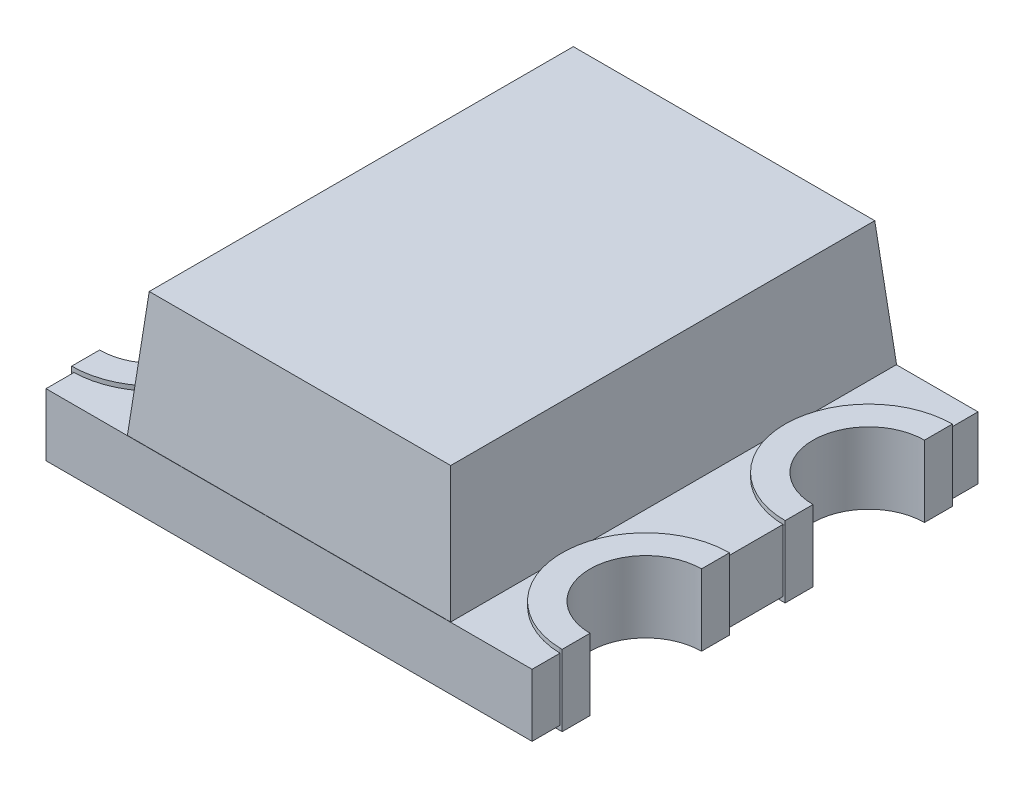
SolidWorks part; units mm, degrees
ref_plane "Front Plane" through (0, 0, 0) normal (0, 0, 1) x (1, 0, 0)
ref_plane "Top Plane" through (0, 0, 0) normal (0, 1, 0) x (1, 0, 0)
ref_plane "Right Plane" through (0, 0, 0) normal (1, 0, 0) x (0, 0, -1)
sketch "Sketch1" plane through (0, 0, 0) normal (0, 1, 0) x (1, 0, 0)
  line L1 (1.1, 1) -> (-1.1, 1)
  line L2 (1.1, 1) -> (1.1, -1)
  line L3 (1.1, -1) -> (-1.1, -1)
  line L4 (-1.1, 1) -> (-1.1, -1)
  line L5 (1.1, 1) -> (-1.1, -1) construction
  line L6 (1.1, -1) -> (-1.1, 1) construction
  point P0 (0, 0)
  dimension "D1" = 2
  dimension "D2" = 2.2
extrude "Boss-Extrude1" add sketch "Sketch1" along normal blind 0.28
sketch "Sketch2" plane through (0, 0.28, 0) normal (0, 1, 0) x (1, 0, 0)
  line L0 (-1.1, 1) -> (-1.1, -1) construction
  line L1 (-1.1, 0.875) -> (-0.565, 0.875)
  line L2 (-1.1, 0.875) -> (-1.1, 0.125)
  line L3 (-1.1, 0.125) -> (-0.565, 0.125)
  line L4 (-0.565, 0.875) -> (-0.565, 0.125)
  line L5 (0, 0) -> (0, 0.3307) construction
  line L6 (0, 0) -> (0.4542, 0) construction
  line L7 (0.565, 0.875) -> (0.565, 0.125)
  line L8 (1.1, 0.125) -> (0.565, 0.125)
  line L9 (1.1, 0.875) -> (1.1, 0.125)
  line L10 (1.1, 0.875) -> (0.565, 0.875)
  line L11 (1.1, -0.875) -> (0.565, -0.875)
  line L12 (1.1, -0.875) -> (1.1, -0.125)
  line L13 (1.1, -0.125) -> (0.565, -0.125)
  line L14 (0.565, -0.875) -> (0.565, -0.125)
  line L15 (-0.565, -0.875) -> (-0.565, -0.125)
  line L16 (-1.1, -0.125) -> (-0.565, -0.125)
  line L17 (-1.1, -0.875) -> (-1.1, -0.125)
  line L18 (-1.1, -0.875) -> (-0.565, -0.875)
  circle A0 centre (-1.1, 0.5) radius 0.25
  circle A1 centre (1.1, 0.5) radius 0.25
  circle A2 centre (1.1, -0.5) radius 0.25
  circle A3 centre (-1.1, -0.5) radius 0.25
  point P9 (-0.565, 0.5)
  line M5 (-1.1, 1) -> (-1.1, -1)
  line M7 (1.1, -1) -> (1.1, 1)
  dimension "D3" = 0.535
  dimension "D4" = 0.5
  dimension "D1" = 0.5
  dimension "D2" = 0.75
extrude "Boss-Extrude2" add sketch "Sketch2" along normal blind 0.02 contours A0 L3 L4 L1 M5 | A1 L10 L7 L8 M7 | A2 L13 L14 L11 M7 | A3 L18 L15 L16 M5
sketch "Sketch3" plane through (0, 0.28, 0) normal (0, 1, 0) x (1, 0, 0)
  line L1 (-1.1, 0.75) -> (-1.1, 0.25)
  line L2 (-1.1, 0.75) -> (-1.1, 0.25)
  line L3 (-1.1, -0.25) -> (-1.1, -0.75)
  line L4 (-1.1, -0.25) -> (-1.1, -0.75)
  line L5 (1.1, 0.25) -> (1.1, 0.75)
  line L6 (1.1, 0.25) -> (1.1, 0.75)
  line L7 (1.1, -0.75) -> (1.1, -0.25)
  line L8 (1.1, -0.75) -> (1.1, -0.25)
  arc A1 (-1.1, 0.25) -> (-1.1, 0.75) centre (-1.1, 0.5) ccw
  arc A2 (-1.1, 0.25) -> (-1.1, 0.75) centre (-1.1, 0.5) ccw
  arc A3 (-1.1, -0.75) -> (-1.1, -0.25) centre (-1.1, -0.5) ccw
  arc A4 (-1.1, -0.75) -> (-1.1, -0.25) centre (-1.1, -0.5) ccw
  arc A5 (1.1, 0.75) -> (1.1, 0.25) centre (1.1, 0.5) ccw
  arc A6 (1.1, 0.75) -> (1.1, 0.25) centre (1.1, 0.5) ccw
  arc A7 (1.1, -0.25) -> (1.1, -0.75) centre (1.1, -0.5) ccw
  arc A8 (1.1, -0.25) -> (1.1, -0.75) centre (1.1, -0.5) ccw
  dimension "D1" = 0
  dimension "D2" = 0
  dimension "D3" = 0
  dimension "D4" = 0
extrude "Cut-Extrude1" cut sketch "Sketch3" against normal blind 2
sketch "Sketch4" plane through (-1.1, 0, 0) normal (-1, 0, 0) x (0, 0, 1)
  line L0 (-0.875, 0.28) -> (-0.875, 0)
  line L1 (-1, 0) -> (-0.75, 0) construction
  line L2 (-0.125, 0.28) -> (-0.125, 0)
  line L3 (-0.25, 0) -> (0.25, 0) construction
  line L4 (0.125, 0.28) -> (0.125, 0)
  line L5 (-0.125, 0.28) -> (0.125, 0.28) construction
  line L6 (0.875, 0.28) -> (0.875, 0)
  line L7 (0.75, 0) -> (1, 0) construction
  line L14 (-1, 0) -> (-0.75, 0)
  line L15 (-0.75, 0) -> (-0.75, 0.3)
  line L16 (-0.25, 0) -> (0.25, 0)
  line L17 (0.25, 0) -> (0.25, 0.3)
  line L18 (0.25, 0.3) -> (0.125, 0.3)
  line L19 (0.125, 0.3) -> (0.125, 0.28)
  line L20 (0.125, 0.28) -> (-0.125, 0.28)
  line L21 (-0.125, 0.28) -> (-0.125, 0.3)
  line L22 (-0.125, 0.3) -> (-0.25, 0.3)
  line L23 (-0.25, 0.3) -> (-0.25, 0)
  line L24 (-0.25, 0) -> (0.25, 0)
  line L25 (0.25, 0) -> (0.25, 0.3)
  line L26 (0.25, 0.3) -> (0.125, 0.3)
  line L27 (0.125, 0.3) -> (0.125, 0.28)
  line L28 (0.125, 0.28) -> (-0.125, 0.28)
  line L29 (-0.125, 0.28) -> (-0.125, 0.3)
  line L30 (-0.125, 0.3) -> (-0.25, 0.3)
  line L31 (-0.25, 0.3) -> (-0.25, 0)
  line L32 (-0.75, 0.3) -> (-0.875, 0.3)
  line L33 (-0.875, 0.3) -> (-0.875, 0.28)
  line L34 (-0.875, 0.28) -> (-1, 0.28)
  line L35 (-1, 0.28) -> (-1, 0)
  line L36 (-1, 0) -> (-0.75, 0)
  line L37 (-0.75, 0) -> (-0.75, 0.3)
  line L38 (-0.75, 0.3) -> (-0.875, 0.3)
  line L39 (-0.875, 0.3) -> (-0.875, 0.28)
  line L40 (-0.875, 0.28) -> (-1, 0.28)
  line L41 (-1, 0.28) -> (-1, 0)
  line L42 (0.75, 0.3) -> (0.75, 0)
  line L43 (0.75, 0) -> (1, 0)
  line L44 (1, 0) -> (1, 0.28)
  line L45 (1, 0.28) -> (0.875, 0.28)
  line L46 (0.875, 0.28) -> (0.875, 0.3)
  line L47 (0.875, 0.3) -> (0.75, 0.3)
  line L48 (0.75, 0.3) -> (0.75, 0)
  line L49 (0.75, 0) -> (1, 0)
  line L50 (1, 0) -> (1, 0.28)
  line L51 (1, 0.28) -> (0.875, 0.28)
  line L52 (0.875, 0.28) -> (0.875, 0.3)
  line L53 (0.875, 0.3) -> (0.75, 0.3)
  line M21 (-1, 0) -> (-0.75, 0)
  line M25 (-0.875, 0.28) -> (-1, 0.28)
  line M26 (-1, 0.28) -> (-1, 0)
  dimension "D1" = 0
  dimension "D2" = 0
  dimension "D3" = 0
extrude "Cut-Extrude2" cut sketch "Sketch4" against normal blind 0.01 contours L0 M25 M26 M21 | L4 L28 L2 L24 | L50 L51 L6 L49
sketch "Sketch5" plane through (1.1, 0, 0) normal (1, 0, 0) x (0, 0, -1)
  line L0 (-0.875, 0.28) -> (-0.875, 0)
  line L1 (-1, 0) -> (-0.75, 0) construction
  line L2 (-0.125, 0.28) -> (-0.125, 0)
  line L3 (-0.25, 0) -> (0.25, 0) construction
  line L4 (0.125, 0.28) -> (0.125, 0)
  line L5 (0.875, 0.28) -> (0.875, 0)
  line L6 (0.75, 0) -> (1, 0) construction
  line L13 (-1, 0) -> (-0.75, 0)
  line L14 (-0.75, 0) -> (-0.75, 0.3)
  line L15 (-0.75, 0.3) -> (-0.875, 0.3)
  line L16 (-0.875, 0.3) -> (-0.875, 0.28)
  line L17 (-0.875, 0.28) -> (-1, 0.28)
  line L18 (-1, 0.28) -> (-1, 0)
  line L19 (-1, 0) -> (-0.75, 0)
  line L20 (-0.75, 0) -> (-0.75, 0.3)
  line L21 (-0.75, 0.3) -> (-0.875, 0.3)
  line L22 (-0.875, 0.3) -> (-0.875, 0.28)
  line L23 (-0.875, 0.28) -> (-1, 0.28)
  line L24 (-1, 0.28) -> (-1, 0)
  line L25 (0.75, 0.3) -> (0.75, 0)
  line L26 (0.75, 0) -> (1, 0)
  line L27 (-0.25, 0) -> (0.25, 0)
  line L28 (0.25, 0) -> (0.25, 0.3)
  line L29 (0.25, 0.3) -> (0.125, 0.3)
  line L30 (0.125, 0.3) -> (0.125, 0.28)
  line L31 (0.125, 0.28) -> (-0.125, 0.28)
  line L32 (-0.125, 0.28) -> (-0.125, 0.3)
  line L33 (-0.125, 0.3) -> (-0.25, 0.3)
  line L34 (-0.25, 0.3) -> (-0.25, 0)
  line L35 (-0.25, 0) -> (0.25, 0)
  line L36 (0.25, 0) -> (0.25, 0.3)
  line L37 (0.25, 0.3) -> (0.125, 0.3)
  line L38 (0.125, 0.3) -> (0.125, 0.28)
  line L39 (0.125, 0.28) -> (-0.125, 0.28)
  line L40 (-0.125, 0.28) -> (-0.125, 0.3)
  line L41 (-0.125, 0.3) -> (-0.25, 0.3)
  line L42 (-0.25, 0.3) -> (-0.25, 0)
  line L43 (1, 0) -> (1, 0.28)
  line L44 (1, 0.28) -> (0.875, 0.28)
  line L45 (0.875, 0.28) -> (0.875, 0.3)
  line L46 (0.875, 0.3) -> (0.75, 0.3)
  line L47 (0.75, 0.3) -> (0.75, 0)
  line L48 (0.75, 0) -> (1, 0)
  line L49 (1, 0) -> (1, 0.28)
  line L50 (1, 0.28) -> (0.875, 0.28)
  line L51 (0.875, 0.28) -> (0.875, 0.3)
  line L52 (0.875, 0.3) -> (0.75, 0.3)
  line M21 (-0.25, 0) -> (0.25, 0)
  line M25 (0.125, 0.28) -> (-0.125, 0.28)
  dimension "D1" = 0
  dimension "D2" = 0
  dimension "D3" = 0
extrude "Cut-Extrude3" cut sketch "Sketch5" against normal blind 0.01 contours L23 L24 L19 L0 | L4 L2 M25 M21 | L49 L50 L5 L48
sketch "Sketch6" plane through (0, 0, 0) normal (0, -1, 0) x (1, 0, 0)
  line L0 (-1.09, 1) -> (1.09, 1) construction
  line L1 (-0.725, 1) -> (0.725, 1)
  line L2 (-0.725, 1) -> (-0.725, -1)
  line L3 (-0.725, -1) -> (0.725, -1)
  line L4 (0.725, 1) -> (0.725, -1)
  line L5 (1.09, -1) -> (-1.09, -1) construction
  dimension "D1" = 1.45
  dimension "D2" = 0.725
extrude "Boss-Extrude3" add sketch "Sketch6" along normal blind 0.56 draft 5
sketch "Sketch8" plane through (0, 0, 0) normal (0, -1, 0) x (1, 0, 0)
  line L1 (-0.725, 1) -> (0.725, 1)
  line L2 (-0.725, 1) -> (-0.725, -1)
  line L3 (-0.725, -1) -> (0.725, -1)
  line L4 (0.725, 1) -> (0.725, -1)
extrude "Cut-Extrude4" cut sketch "Sketch8" along normal blind 0.001
sketch "Sketch10" plane through (0, 0, 0) normal (0, -1, 0) x (1, 0, 0)
  line L0 (-1.09, 1) -> (1.09, 1) construction
  line L1 (-0.3, -0.04) -> (0.39, -0.04)
  line L2 (-0.3, -0.04) -> (-0.3, 0.5)
  line L3 (-0.3, 0.5) -> (0.39, 0.5)
  line L4 (0.39, -0.04) -> (0.39, 0.5)
  line L5 (-1.1, 0.125) -> (-1.1, 0.25) construction
  dimension "D1" = 0.5
  dimension "D2" = 0.54
  dimension "D3" = 0.69
  dimension "D4" = 0.8
extrude "Boss-Extrude5" add sketch "Sketch10" along normal blind 0.2
sketch "Sketch11" plane through (0, -0.001, 0) normal (0, 1, 0) x (1, 0, 0)
  line L0 (-0.3, -0.5) -> (-0.3, 0.04) construction
  line L1 (-0.3, -0.5) -> (0.39, -0.5)
  line L2 (-0.3, -0.5) -> (-0.3, 0.04)
  line L3 (-0.3, 0.04) -> (0.39, 0.04)
  line L4 (0.39, -0.5) -> (0.39, 0.04)
  line L5 (0.39, -0.5) -> (-0.3, -0.5) construction
  line L6 (-0.31, -0.51) -> (-0.31, 0.05)
  line L7 (-0.31, 0.05) -> (0.4, 0.05)
  line L8 (0.4, -0.51) -> (0.4, 0.05)
  line L9 (-0.31, -0.51) -> (0.4, -0.51)
  line M5 (0.39, -0.5) -> (-0.3, -0.5)
  line M6 (-0.3, -0.5) -> (-0.3, 0.04)
  line M7 (-0.3, 0.04) -> (0.39, 0.04)
  line M8 (0.39, 0.04) -> (0.39, -0.5)
  dimension "D1" = 0.01
extrude "Cut-Extrude5" cut sketch "Sketch11" against normal blind 0.201 contours M5 M8 M7 M6 | L6 L9 L8 L7 M8 M5 M6 M7
sketch "Sketch9" plane through (0, 0, 0) normal (0, -1, 0) x (1, 0, 0)
  line L24 (-1.09, -0.875) -> (-1.09, -1)
  line L25 (-1.09, -1) -> (1.09, -1)
  line L26 (1.09, -1) -> (1.09, -0.875)
  line L27 (1.09, -0.875) -> (1.1, -0.875)
  line L28 (1.1, -0.875) -> (1.1, -0.75)
  line L29 (1.1, -0.25) -> (1.1, -0.125)
  line L30 (1.1, -0.125) -> (1.09, -0.125)
  line L31 (1.09, -0.125) -> (1.09, 0.125)
  line L32 (1.09, 0.125) -> (1.1, 0.125)
  line L33 (1.1, 0.125) -> (1.1, 0.25)
  line L34 (1.1, 0.75) -> (1.1, 0.875)
  line L35 (1.1, 0.875) -> (1.09, 0.875)
  line L36 (1.09, 0.875) -> (1.09, 1)
  line L37 (1.09, 1) -> (-1.09, 1)
  line L38 (-1.09, 1) -> (-1.09, 0.875)
  line L39 (-1.09, 0.875) -> (-1.1, 0.875)
  line L40 (-1.1, 0.875) -> (-1.1, 0.75)
  line L41 (-1.1, 0.25) -> (-1.1, 0.125)
  line L42 (-1.1, 0.125) -> (-1.09, 0.125)
  line L43 (-1.09, 0.125) -> (-1.09, -0.125)
  line L44 (-1.09, -0.125) -> (-1.1, -0.125)
  line L45 (-1.1, -0.125) -> (-1.1, -0.25)
  line L46 (-1.1, -0.75) -> (-1.1, -0.875)
  line L47 (-1.1, -0.875) -> (-1.09, -0.875)
  line L48 (-1.09, -0.875) -> (-1.09, -1)
  line L49 (-1.09, -1) -> (1.09, -1)
  line L50 (1.09, -1) -> (1.09, -0.875)
  line L51 (1.09, -0.875) -> (1.1, -0.875)
  line L52 (1.1, -0.875) -> (1.1, -0.75)
  line L53 (1.1, -0.25) -> (1.1, -0.125)
  line L54 (1.1, -0.125) -> (1.09, -0.125)
  line L55 (1.09, -0.125) -> (1.09, 0.125)
  line L56 (1.09, 0.125) -> (1.1, 0.125)
  line L57 (1.1, 0.125) -> (1.1, 0.25)
  line L58 (1.1, 0.75) -> (1.1, 0.875)
  line L59 (1.1, 0.875) -> (1.09, 0.875)
  line L60 (1.09, 0.875) -> (1.09, 1)
  line L61 (1.09, 1) -> (-1.09, 1)
  line L62 (-1.09, 1) -> (-1.09, 0.875)
  line L63 (-1.09, 0.875) -> (-1.1, 0.875)
  line L64 (-1.1, 0.875) -> (-1.1, 0.75)
  line L65 (-1.1, 0.25) -> (-1.1, 0.125)
  line L66 (-1.1, 0.125) -> (-1.09, 0.125)
  line L67 (-1.09, 0.125) -> (-1.09, -0.125)
  line L68 (-1.09, -0.125) -> (-1.1, -0.125)
  line L69 (-1.1, -0.125) -> (-1.1, -0.25)
  line L70 (-1.1, -0.75) -> (-1.1, -0.875)
  line L71 (-1.1, -0.875) -> (-1.09, -0.875)
  arc A0 (-1.1, 0.125) -> (-1.1, 0.875) centre (-1.1, 0.5) ccw
  arc A1 (-1.1, -0.875) -> (-1.1, -0.125) centre (-1.1, -0.5) ccw
  arc A2 (1.1, 0.875) -> (1.1, 0.125) centre (1.1, 0.5) ccw
  arc A3 (1.09, -0.125) -> (1.09, -0.875) centre (1.1, -0.5) ccw
  arc A8 (1.1, -0.25) -> (1.1, -0.75) centre (1.1, -0.5) ccw
  arc A9 (1.1, 0.75) -> (1.1, 0.25) centre (1.1, 0.5) ccw
  arc A10 (-1.1, 0.25) -> (-1.1, 0.75) centre (-1.1, 0.5) ccw
  arc A11 (-1.1, -0.75) -> (-1.1, -0.25) centre (-1.1, -0.5) ccw
  arc A12 (1.1, -0.25) -> (1.1, -0.75) centre (1.1, -0.5) ccw
  arc A13 (1.1, 0.75) -> (1.1, 0.25) centre (1.1, 0.5) ccw
  arc A14 (-1.1, 0.25) -> (-1.1, 0.75) centre (-1.1, 0.5) ccw
  arc A15 (-1.1, -0.75) -> (-1.1, -0.25) centre (-1.1, -0.5) ccw
  line M33 (1.09, -0.875) -> (1.1, -0.875)
  line M34 (1.1, -0.875) -> (1.1, -0.75)
  arc M35 (1.1, -0.75) -> (1.1, -0.25) centre (1.1, -0.5) cw
  line M36 (1.1, -0.25) -> (1.1, -0.125)
  line M37 (1.1, -0.125) -> (1.09, -0.125)
  line M40 (1.1, 0.125) -> (1.1, 0.25)
  arc M41 (1.1, 0.25) -> (1.1, 0.75) centre (1.1, 0.5) cw
  line M42 (1.1, 0.75) -> (1.1, 0.875)
  line M48 (-1.1, 0.875) -> (-1.1, 0.75)
  arc M49 (-1.1, 0.75) -> (-1.1, 0.25) centre (-1.1, 0.5) cw
  line M50 (-1.1, 0.25) -> (-1.1, 0.125)
  line M54 (-1.1, -0.125) -> (-1.1, -0.25)
  arc M55 (-1.1, -0.25) -> (-1.1, -0.75) centre (-1.1, -0.5) cw
  line M56 (-1.1, -0.75) -> (-1.1, -0.875)
  dimension "D2" = 0
extrude "Boss-Extrude4" add sketch "Sketch9" along normal blind 0.02 contours A0 M50 M48 M49 | A1 M56 M54 M55 | A2 M42 M40 M41 | A3 M37 M33 M34 M35 M36
sketch "Sketch12" plane through (0, 0.28, 0) normal (0, 1, 0) x (1, 0, 0)
  line L0 (0.315, 0.675) -> (0.315, -0.675) construction
  line L1 (0.515, 0.675) -> (0.515, -0.675)
  line L2 (0.115, 0.675) -> (0.115, -0.675)
  line L3 (0.565, 0.875) -> (0.565, 0.125) construction
  line L4 (1.09, 0.875) -> (0.565, 0.875) construction
  arc A0 (0.515, 0.675) -> (0.115, 0.675) centre (0.315, 0.675) ccw
  arc A1 (0.115, -0.675) -> (0.515, -0.675) centre (0.315, -0.675) ccw
  point P2 (0.315, 0)
  dimension "D1" = 0.25
  dimension "D2" = 0
  dimension "D3" = 0.2
extrude "Boss-Extrude6" add sketch "Sketch12" along normal blind 0.02
move or copy body "Body-Move/Copy1" bodies to move or copy 113 copy no rotation origin (0, 0, 0) rotation axis (-1, 0, 0) rotation angle 90
move or copy body "Body-Move/Copy2" bodies to move or copy 114 copy no translate (0, 0, 0.28)
move or copy body "Body-Move/Copy3" bodies to move or copy 115 copy no rotation origin (0, 0, 0) rotation axis (-1, 0, 0) rotation angle 90
